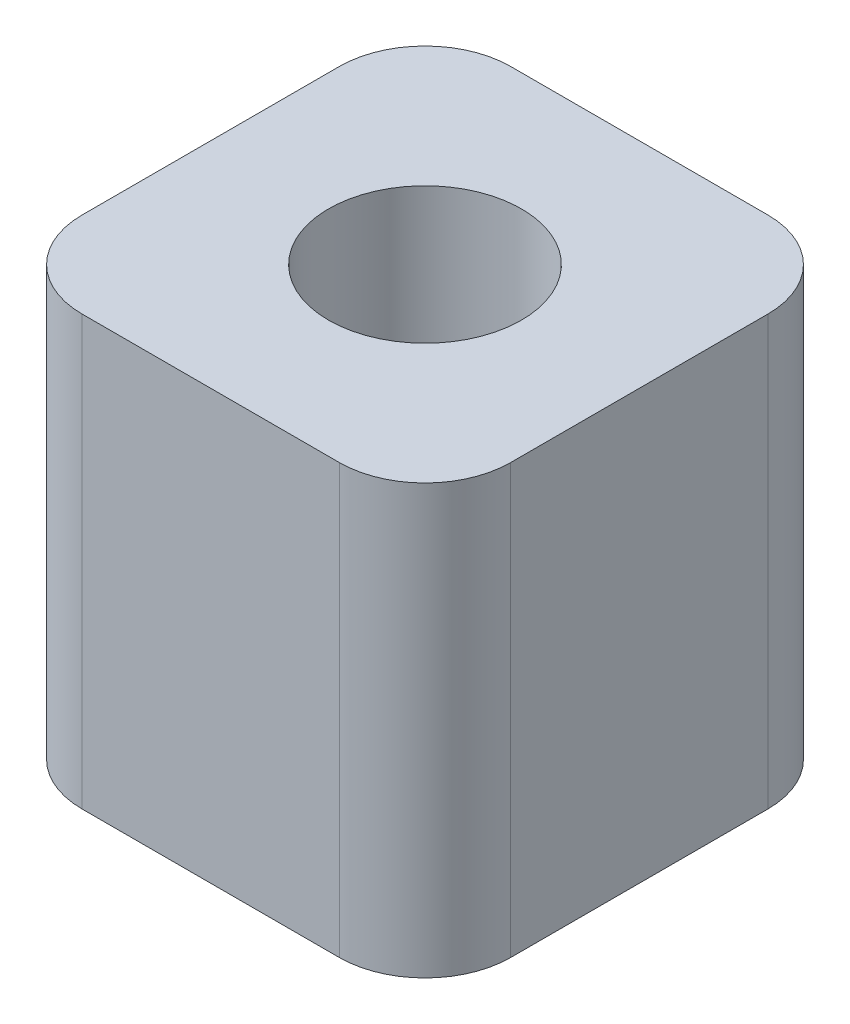
SolidWorks part; units mm, degrees
ref_plane "Front" through (0, 0, 0) normal (0, 0, 1) x (1, 0, 0)
ref_plane "Top" through (0, 0, 0) normal (0, 1, 0) x (1, 0, 0)
ref_plane "Right" through (0, 0, 0) normal (1, 0, 0) x (0, 0, -1)
sketch "Sketch1" plane through (0, 0, 0) normal (0, 1, 0) x (1, 0, 0)
  line L1 (-5, -5) -> (5, -5)
  line L2 (-5, -5) -> (-5, 5)
  line L3 (-5, 5) -> (5, 5)
  line L4 (5, -5) -> (5, 5)
  line L5 (-5, -5) -> (5, 5) construction
  line L6 (-5, 5) -> (5, -5) construction
  circle A0 centre (0, 0) radius 2.25
  point P0 (0, 0)
  dimension "D3" = 4.5
  dimension "D1" = 10
  dimension "D2" = 10
extrude "Boss-Extrude1" add sketch "Sketch1" along normal blind 10
fillet "Fillet1" radius 2 4 edges at (-5, 5, 5) (-5, 5, -5) (5, 5, -5) (5, 5, 5)
equation "\"D2@Sketch1\"=\"D1@Sketch1\""
